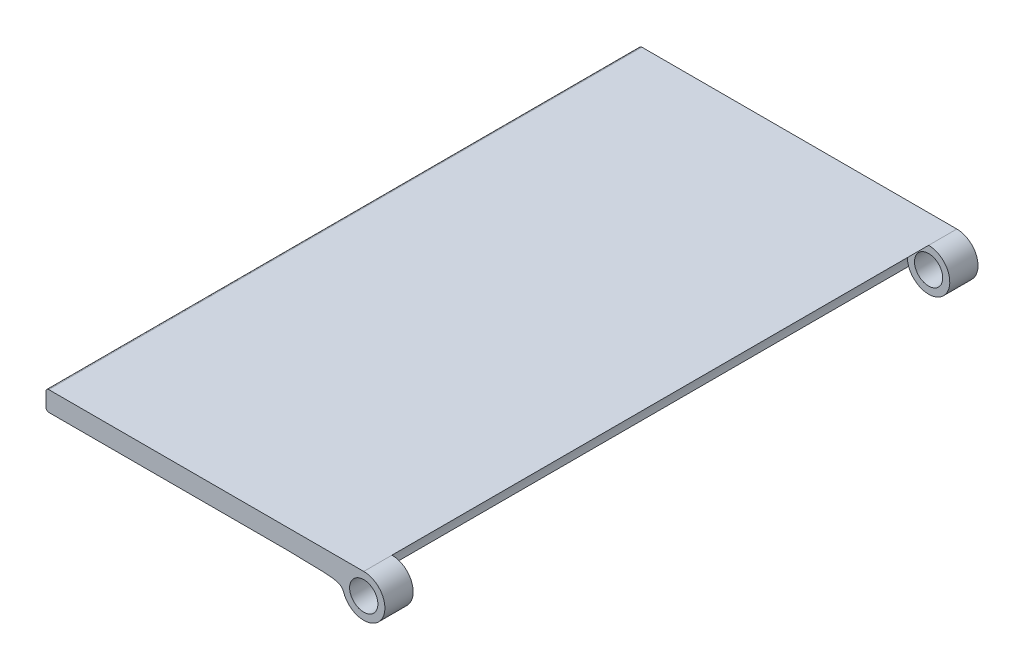
SolidWorks part; units mm, degrees
ref_plane "Front" through (0, 0, 0) normal (0, 0, 1) x (1, 0, 0)
ref_plane "Top" through (0, 0, 0) normal (0, 1, 0) x (1, 0, 0)
ref_plane "Right" through (0, 0, 0) normal (1, 0, 0) x (0, 0, -1)
sketch "草图1" plane through (0, 0, 0) normal (0, 0, 1) x (1, 0, 0)
  line L0 (112.7381, 241.1408) -> (1063.4047, 241.1408) construction
  line L1 (-1000, 0) -> (49000, 0) construction
  line L2 (-992.7821, 15) -> (49007.2179, 15) construction
  line L3 (0, -1000) -> (0, 5) construction
  line L4 (120, -895.6152) -> (120, 49104.3848) construction
  line L5 (210.9503, 181.969) -> (1161.617, 181.969) construction
  line L6 (1, 8) -> (85, 8)
  line L7 (1, 0) -> (120, 0)
  line L8 (0, 1) -> (0, 4)
  line L9 (1, 15) -> (120, 15)
  line L10 (120, 0) -> (120, 15)
  line L11 (85, 8) -> (85, 15)
  line L12 (1, 5) -> (100.0741, 5)
  line L13 (85, 8) -> (102.8741, 7.7512) construction
  line L14 (102.8741, 7.7512) -> (104.3164, 7.7535) construction
  line L16 (104.3164, 7.7535) -> (105.4289, 5) construction
  line L17 (0, 8) -> (0, 49000) construction
  line L18 (0, 9) -> (0, 14)
  line L19 (100.0741, 5) -> (105.4289, 5)
  circle A0 centre (112.5, 7.5) radius 7.5
  arc A1 (1, 0) -> (0, 1) centre (1, 1) cw
  arc A2 (1, 5) -> (0, 4) centre (1, 4) ccw
  arc A3 (0, 14) -> (1, 15) centre (1, 14) cw
  arc A4 (1, 8) -> (0, 9) centre (1, 9) cw
  circle A5 centre (112.5, 7.5) radius 5
  spline S0 degree 3 poles (85, 8) (102.8741, 7.7512) (104.3164, 7.7535) (105.4289, 5) knots 0 0 0 0 1 1 1 1
  point P23 (104.3164, 7.7535)
  point P25 (102.9572, 6.8959)
  point P30 (0, 0)
  point P36 (0, 15)
  point P41 (95.5947, 9.2584)
  point P42 (0, 0)
  point P43 (0, 0)
  point P44 (102.8741, 7.7512)
  dimension "D1" = 120
  dimension "D3" = 120
  dimension "D7" = 15
  dimension "D11" = 1
  dimension "D10" = 10
  dimension "D2" = 15
  dimension "D4" = 15
  dimension "D5" = 7
  dimension "D6" = 85
  dimension "D8" = 7.5
  dimension "D9" = 7.5
extrude "凸台-拉伸4" add sketch "草图1" along normal blind 210
ref_plane "基准面1" through (0, 0, 105) normal (0, 0, -1) x (-1, 0, 0)
sketch "草图3" plane through (0, 0, 105) normal (0, 0, -1) x (-1, 0, 0)
  circle A0 centre (-112.5, 7.5) radius 7.5
  dimension "D1" = 15
extrude "切除-拉伸3" cut sketch "草图3" against normal blind 95 and the other way blind 95
